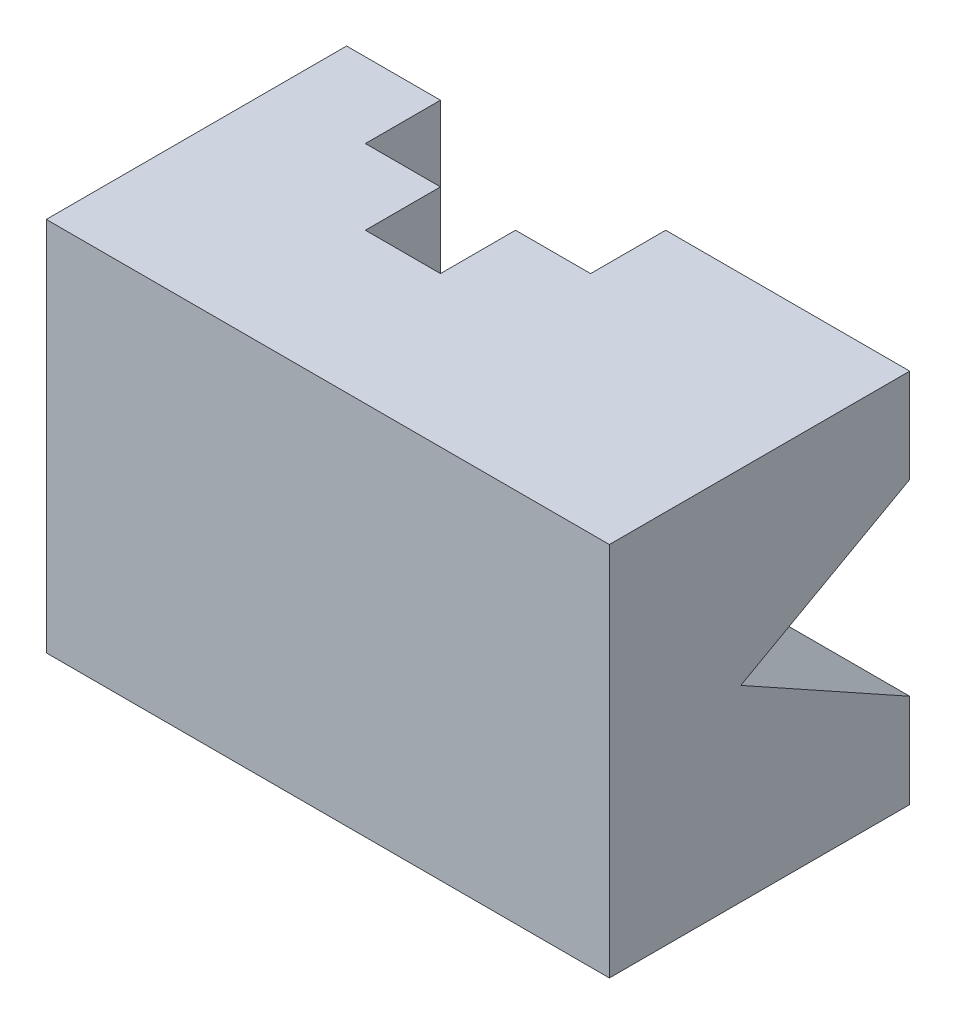
SolidWorks part; units mm, degrees
ref_plane "Front Plane" through (0, 0, 0) normal (0, 0, 1) x (1, 0, 0)
ref_plane "Top Plane" through (0, 0, 0) normal (0, 1, 0) x (1, 0, 0)
ref_plane "Right Plane" through (0, 0, 0) normal (1, 0, 0) x (0, 0, -1)
sketch "Sketch1" plane through (0, 0, 0) normal (0, 1, 0) x (1, 0, 0)
  line L0 (-50, 40) -> (-50, 20)
  line L1 (-75, -40) -> (75, -40)
  line L2 (-75, -40) -> (-75, 40)
  line L3 (-75, 40) -> (75, 40)
  line L4 (75, -40) -> (75, 40)
  line L5 (-75, -40) -> (75, 40) construction
  line L6 (-75, 40) -> (75, -40) construction
  line L7 (-50, 20) -> (-30, 20)
  line L8 (-30, 20) -> (-30, 0)
  line L9 (-30, 0) -> (-10, 0)
  line L10 (-10, 0) -> (-10, 20)
  line L11 (-10, 20) -> (10, 20)
  line L12 (10, 20) -> (10, 40)
  line L13 (-50, 40) -> (-75, 40)
  point P0 (0, 0)
  dimension "D1" = 80
  dimension "D2" = 150
  dimension "D3" = 25
  dimension "D4" = 20
extrude "Boss-Extrude1" add sketch "Sketch1" along normal blind 100 contours L12 L11 L10 L9 L8 L7 L0 L3 L2 L1 L4
sketch "Sketch3" plane through (75, 0, 0) normal (1, 0, 0) x (0, 0, -1)
  line L0 (40, 50) -> (-7.522, 50) construction
  line L1 (40, 100) -> (40, 0) construction
  line L2 (44.6219, 50) -> (24.3801, 50) construction
  line L3 (40, 75) -> (-5, 50)
  line L4 (40, 25) -> (-5, 50)
  line L7 (40, 25) -> (40, 75)
  line L9 (-40, 100) -> (40, 100) construction
  point P10 (-5, 52.6122)
  dimension "D1" = 25
  dimension "D2" = 45
extrude "Cut-Extrude2" cut sketch "Sketch3" against normal blind 50
